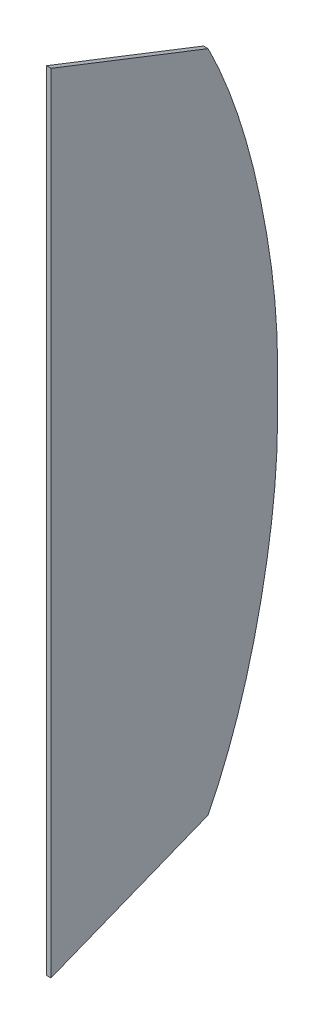
SolidWorks part; units mm, degrees
ref_plane "Спереди" through (0, 0, 0) normal (0, 0, 1) x (1, 0, 0)
ref_plane "Сверху" through (0, 0, 0) normal (0, 1, 0) x (1, 0, 0)
ref_plane "Справа" through (0, 0, 0) normal (1, 0, 0) x (0, 0, -1)
sketch "Эскиз1" plane through (0, 0, 0) normal (1, 0, 0) x (0, 0, -1)
  line L0 (-455, -523) -> (-455, 523) construction
  line L1 (-243, -438.6617) -> (-243, 440) construction
  line L2 (-455, -516.5426) -> (-455, 516.5565)
  line L3 (-455, 516.5565) -> (-249, 435.9056)
  line L4 (-455, -516.5426) -> (-249, -434.5913)
  line L5 (-449, 514.2075) -> (-249, 435.9056) construction
  line L6 (-449, -514.1557) -> (-449, 514.2075) construction
  line L7 (-449, -514.1557) -> (-249, -434.5913) construction
  line L8 (-455, -523) -> (-243, -438.6617) construction
  line L9 (-249, -434.5913) -> (-249, 435.9056) construction
  line L10 (-455, 523) -> (-243, 440) construction
  spline S2 degree 3 poles (-249, 435.9056) (-244.8122, 427.5807) (-236.8014, 410.7383) (-222.2124, 376.4639) (-206.4721, 332.5736) (-191.0652, 278.6225) (-178.6184, 223.742) (-168.6012, 168.3762) (-162.6642, 121.9958) (-159.5885, 84.7804) (-158.191, 56.8473) (-157.6991, 28.8204) (-157.6682, 0.6571) (-157.6991, -27.5061) (-158.191, -55.533) (-159.5885, -83.4661) (-162.6642, -120.6815) (-168.6012, -167.0619) (-178.6184, -222.4277) (-191.0652, -277.3082) (-206.4721, -331.2593) (-222.2124, -375.1496) (-236.8014, -409.424) (-244.8122, -426.2664) (-249, -434.5913) knots 0.002534 0.002534 0.002534 0.002534 0.033626 0.064718 0.126901 0.189084 0.251267 0.31345 0.375634 0.406725 0.437817 0.468908 0.5 0.531092 0.562183 0.593275 0.624366 0.68655 0.748733 0.810916 0.873099 0.935282 0.966374 0.997466 0.997466 0.997466 0.997466
  dimension "D1" = 6
extrude "Бобышка-Вытянуть3" add sketch "Эскиз1" along normal blind 6
